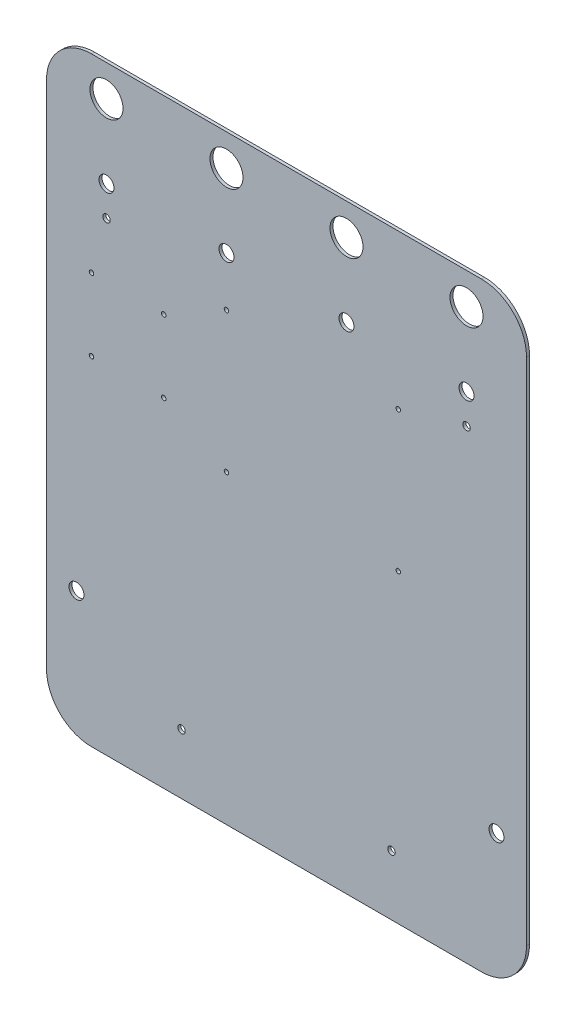
SolidWorks part; units mm, degrees
ref_plane "前视基准面" through (0, 0, 0) normal (0, 0, 1) x (1, 0, 0)
ref_plane "上视基准面" through (0, 0, 0) normal (0, 1, 0) x (1, 0, 0)
ref_plane "右视基准面" through (0, 0, 0) normal (1, 0, 0) x (0, 0, -1)
sketch "草图1" plane through (0, 0, 0) normal (0, 0, 1) x (1, 0, 0)
  line L1 (-200.597, 350) -> (59.403, 350)
  line L2 (-230.597, 320) -> (-230.597, -20)
  line L3 (-200.597, -50) -> (59.403, -50)
  line L4 (89.403, 320) -> (89.403, -20)
  line L5 (-230.597, 350) -> (89.403, -50) construction
  line L6 (-230.597, -50) -> (89.403, 350) construction
  circle A0 centre (-190.5948, 260.0026) radius 2.5
  circle A1 centre (49.4052, 260.0026) radius 2.5
  circle A2 centre (-140.5948, -9.9974) radius 2.5
  circle A3 centre (-0.5948, -9.9974) radius 2.5
  arc A4 (59.403, -50) -> (89.403, -20) centre (59.403, -20) ccw
  arc A5 (-230.597, -20) -> (-200.597, -50) centre (-200.597, -20) ccw
  arc A6 (59.403, 350) -> (89.403, 320) centre (59.403, 320) cw
  arc A7 (-200.597, 350) -> (-230.597, 320) centre (-200.597, 320) ccw
  circle A8 centre (-110.597, 329) radius 11
  circle A9 centre (-30.597, 329) radius 11
  circle A10 centre (-190.597, 329) radius 11
  circle A11 centre (49.403, 329) radius 11
  circle A12 centre (-210.597, 35) radius 5
  circle A13 centre (69.403, 35) radius 5
  circle A14 centre (-110.5993, 247.1047) radius 1.5
  circle A15 centre (-110.5993, 153.6047) radius 1.5
  circle A16 centre (3.9007, 153.6047) radius 1.5
  circle A17 centre (3.9007, 247.1047) radius 1.5
  circle A18 centre (-200.5981, 223.6694) radius 1.5
  circle A19 centre (-152.3981, 223.6694) radius 1.5
  circle A20 centre (-200.5981, 175.4694) radius 1.5
  circle A21 centre (-152.3981, 175.4694) radius 1.5
  circle A23 centre (-30.597, 280) radius 5
  circle A25 centre (-190.5948, 280) radius 5
  circle A26 centre (-110.5993, 280) radius 5
  circle A27 centre (49.4052, 280) radius 5
  point P0 (-70.597, 150)
  dimension "D11" = 30
  dimension "D12" = 80
  dimension "D15" = 21
  dimension "D16" = 85
  dimension "D20" = 10
  dimension "D21" = 10
  dimension "D22" = 5
  dimension "D23" = 5
  dimension "D24" = 22
  dimension "D25" = 22
  dimension "D26" = 22
  dimension "D27" = 22
  dimension "D28" = 119.9977
  dimension "D30" = 114.5
  dimension "D33" = 3
  dimension "D31" = 3
  dimension "D32" = 3
  dimension "D34" = 3
  dimension "D35" = 3
  dimension "D36" = 3
  dimension "D37" = 3
  dimension "D38" = 3
  dimension "D39" = 5
  dimension "D40" = 5
  dimension "D44" = 10
  dimension "D46" = 10
  dimension "D47" = 10
  dimension "D50" = 40.0022
  dimension "D45" = 10
  dimension "D1" = 400
  dimension "D2" = 320
  dimension "D3" = 89.9974
  dimension "D4" = 40.0022
  dimension "D5" = 90.0022
  dimension "D6" = 40.0026
  dimension "D7" = 89.9978
  dimension "D8" = 40.0026
  dimension "D9" = 89.9974
  dimension "D10" = 39.9978
  dimension "D13" = 80
  dimension "D14" = 80
  dimension "D17" = 20
  dimension "D18" = 85
  dimension "D19" = 20
  dimension "D29" = 93.5
  dimension "D41" = 29.9989
  dimension "D42" = 48.2
  dimension "D43" = 48.2
  dimension "D48" = 39.9978
  dimension "D49" = 70
  dimension "D51" = 79.9955
  dimension "D52" = 80.0023
  dimension "D53" = 80.0022
extrude "凸台-拉伸1" add sketch "草图1" along normal blind 2
